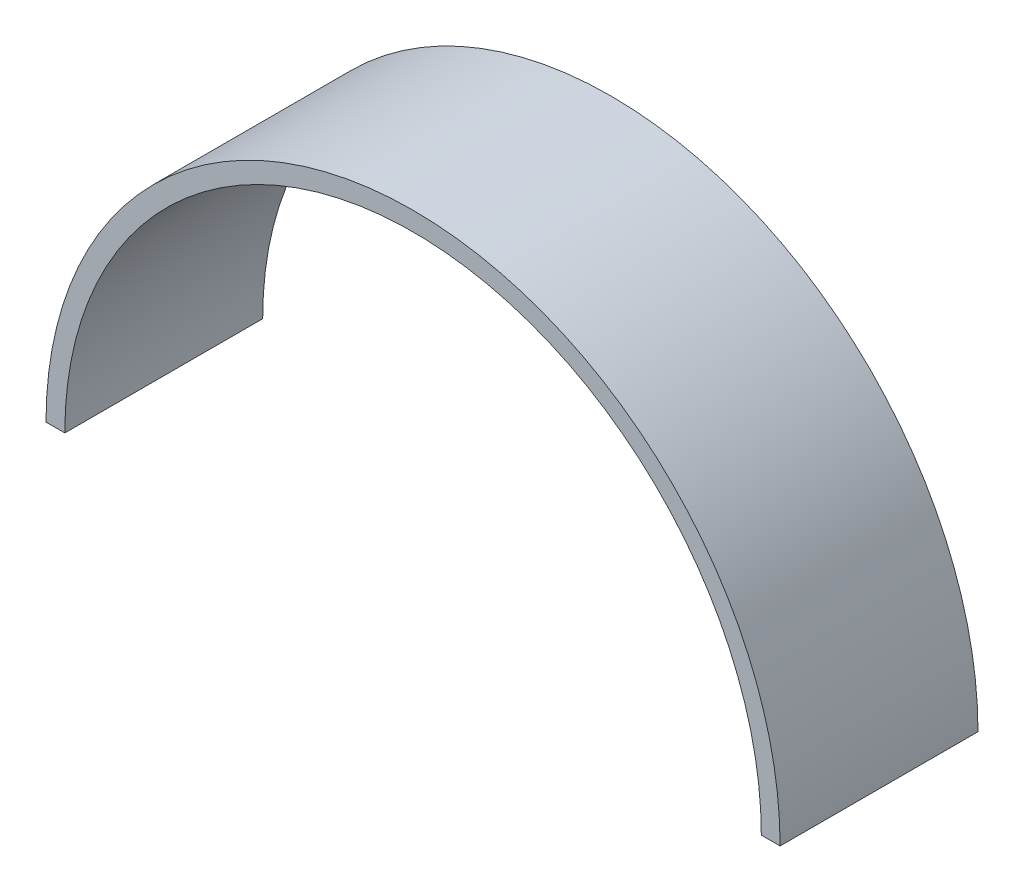
SolidWorks part; units mm, degrees
material "Rubber"
ref_plane "Front Plane" through (0, 0, 0) normal (0, 0, 1) x (1, 0, 0)
ref_plane "Top Plane" through (0, 0, 0) normal (0, 1, 0) x (1, 0, 0)
ref_plane "Right Plane" through (0, 0, 0) normal (1, 0, 0) x (0, 0, -1)
sketch "Sketch1" plane through (0, 0, 0) normal (0, 0, 1) x (1, 0, 0)
  line L0 (-47.117, 0) -> (-44.704, 0)
  line L1 (44.704, 0) -> (47.117, 0)
  line L2 (-47.117, 0) -> (47.117, 0) construction
  arc A0 (47.117, 0) -> (-47.117, 0) centre (0, 0) ccw
  arc A1 (44.704, 0) -> (-44.704, 0) centre (0, 0) ccw
  dimension "D1" = 94.234
  dimension "D2" = 89.408
extrude "Boss-Extrude1" add sketch "Sketch1" along normal blind 25.4
